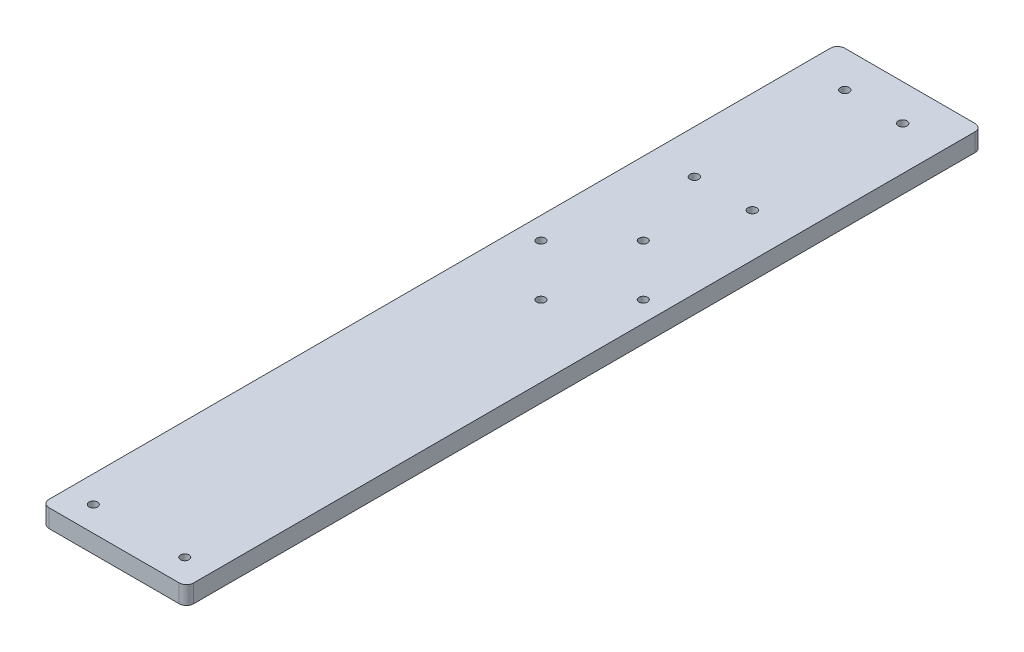
SolidWorks part; units mm, degrees
ref_plane "Front Plane" through (0, 0, 0) normal (0, 0, 1) x (1, 0, 0)
ref_plane "Top Plane" through (0, 0, 0) normal (0, 1, 0) x (1, 0, 0)
ref_plane "Right Plane" through (0, 0, 0) normal (1, 0, 0) x (0, 0, -1)
sketch "Sketch1" plane through (0, 0, 0) normal (0, 1, 0) x (1, 0, 0)
  line L1 (2.54, 0) -> (48.26, 0)
  line L2 (0, 2.54) -> (0, 276.86)
  line L3 (2.54, 279.4) -> (48.26, 279.4)
  line L4 (50.8, 2.54) -> (50.8, 276.86)
  arc A0 (2.54, 0) -> (0, 2.54) centre (2.54, 2.54) cw
  arc A1 (48.26, 0) -> (50.8, 2.54) centre (48.26, 2.54) ccw
  arc A2 (48.26, 279.4) -> (50.8, 276.86) centre (48.26, 276.86) cw
  arc A3 (0, 276.86) -> (2.54, 279.4) centre (2.54, 276.86) cw
  point P7 (0, 0)
  dimension "D3" = 2.54
  dimension "D1" = 50.8
  dimension "D2" = 279.4
extrude "Boss-Extrude1" add sketch "Sketch1" along normal blind 6.35
sketch "Sketch2" plane through (0, 0, 0) normal (0, -1, 0) x (1, 0, 0)
  circle A2 centre (25.6621, -185.525) radius 1.5
  circle A4 centre (43.6226, -167.5645) radius 1.5
  circle A6 centre (7.7016, -167.5645) radius 1.5
  circle A8 centre (25.6621, -149.604) radius 1.5
  circle A10 centre (41.45, -8.7585) radius 1.5
  circle A12 centre (9.35, -8.7585) radius 1.5
extrude "Cut-Extrude1" cut sketch "Sketch2" against normal blind 6.35
sketch "Sketch3" plane through (0, 0, 0) normal (0, -1, 0) x (1, 0, 0)
  circle A2 centre (15.24, -266.7) radius 1.55
  circle A4 centre (35.56, -266.7) radius 1.55
  circle A6 centre (15.24, -213.9) radius 1.55
  circle A8 centre (35.56, -213.9) radius 1.55
extrude "Cut-Extrude2" cut sketch "Sketch3" against normal blind 6.35
